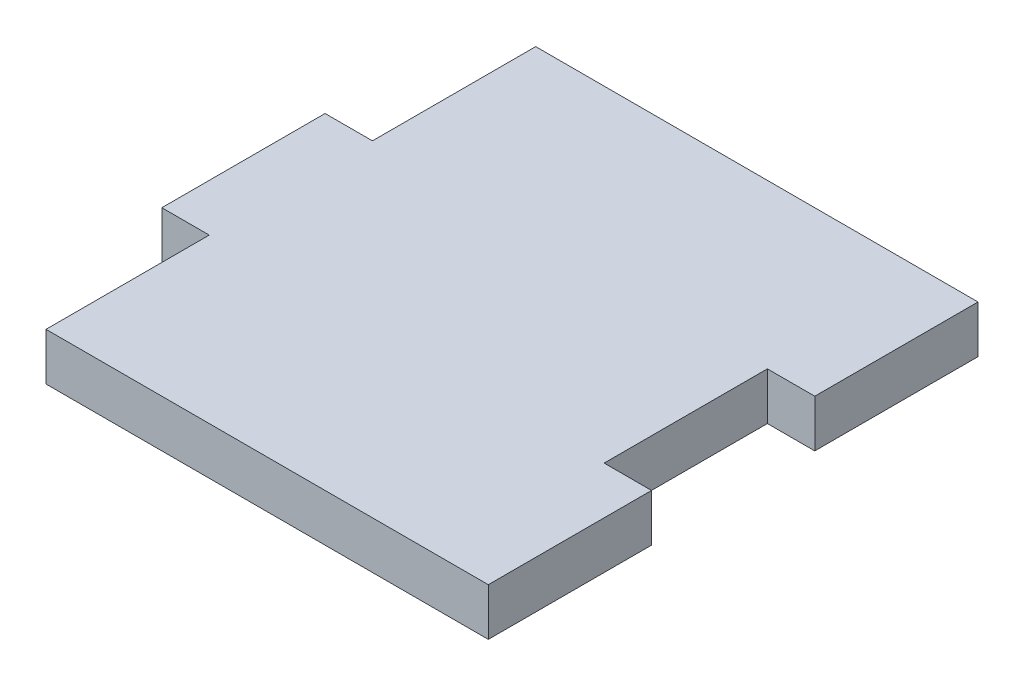
SolidWorks part; units mm, degrees
ref_plane "Front Plane" through (0, 0, 0) normal (0, 0, 1) x (1, 0, 0)
ref_plane "Top Plane" through (0, 0, 0) normal (0, 1, 0) x (1, 0, 0)
ref_plane "Right Plane" through (0, 0, 0) normal (1, 0, 0) x (0, 0, -1)
sketch "Sketch1" plane through (0, 0, 0) normal (0, 1, 0) x (1, 0, 0)
  line L0 (-21, 0) -> (-21, -15.5)
  line L1 (-21, 31) -> (21, 31)
  line L2 (-25.5, 15.5) -> (-25.5, 0)
  line L3 (16.5, -31) -> (4.5, -31)
  line L4 (-21, -31) -> (-21, -35.5)
  line L5 (0, -31) -> (0, -35.5)
  line L6 (16.5, -31) -> (16.5, -15.5)
  line L7 (-16.5, -31) -> (0, -31)
  line L8 (16.5, 0) -> (21, 0)
  line L9 (-21, -35.5) -> (-16.5, -35.5)
  line L12 (-16.5, -35.5) -> (-16.5, -31)
  line L17 (0, -35.5) -> (4.5, -35.5)
  line L20 (4.5, -35.5) -> (4.5, -31)
  line L27 (16.5, -15.5) -> (21, -15.5)
  line L30 (21, -15.5) -> (21, 0)
  line L34 (16.5, 0) -> (16.5, 15.5)
  line L35 (16.5, 15.5) -> (21, 15.5)
  line L38 (21, 15.5) -> (21, 31)
  line L40 (-21, 31) -> (-21, 15.5)
  line L43 (-25.5, 15.5) -> (-21, 15.5)
  line L47 (-25.5, 0) -> (-21, 0)
  line L51 (-21, -15.5) -> (-25.5, -15.5)
  line L53 (-21, -31) -> (-25.5, -31)
  line L55 (-25.5, -15.5) -> (-25.5, -31)
  dimension "D1" = 42
  dimension "D2" = 4.5
  dimension "D3" = 4.5
  dimension "D4" = 4.5
  dimension "D5" = 4.5
  dimension "D6" = 4.5
  dimension "D7" = 4.5
  dimension "D8" = 62
  dimension "D9" = 12
extrude "Boss-Extrude1" add sketch "Sketch1" along normal blind 4.5
sketch "Sketch2" plane through (0, 4.5, 0) normal (0, 1, 0) x (1, 0, 0)
  line L1 (-25.5, -15.5) -> (25.7556, -15.5)
  line L2 (-25.5, -15.5) -> (-25.5, -46.0472)
  line L3 (-25.5, -46.0472) -> (25.7556, -46.0472)
  line L4 (25.7556, -15.5) -> (25.7556, -46.0472)
extrude "Cut-Extrude1" cut sketch "Sketch2" against normal through all
